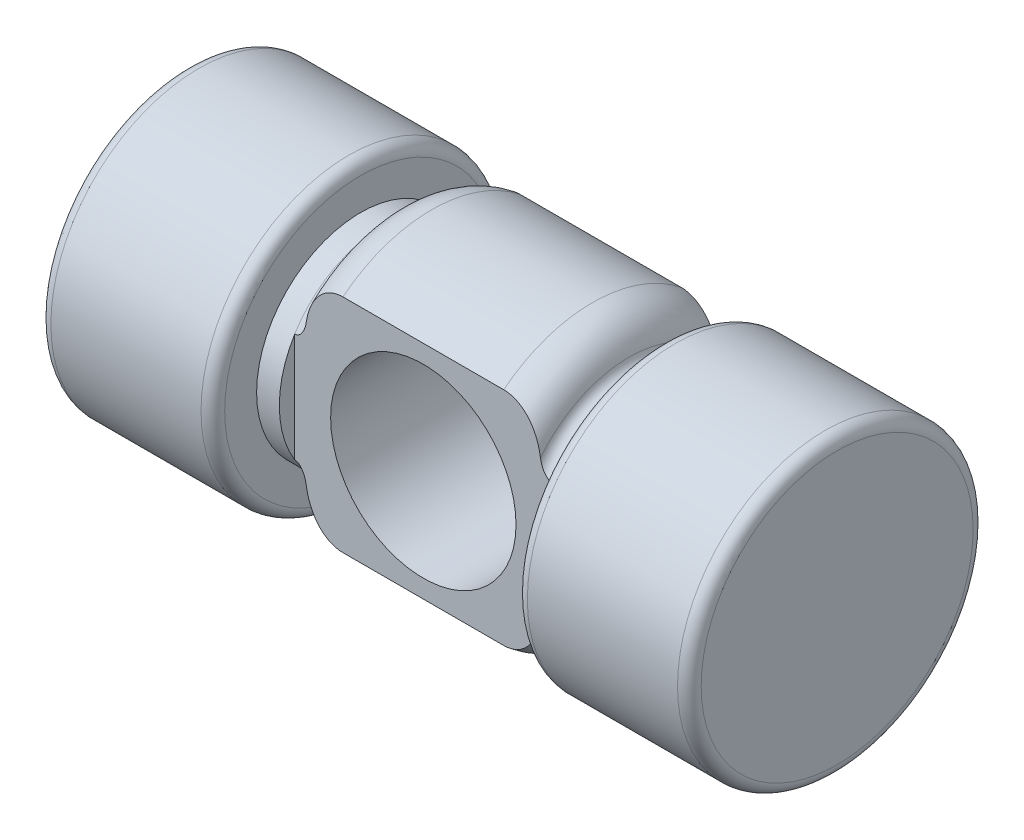
SolidWorks part; units mm, degrees
ref_plane "Front" through (0, 0, 0) normal (0, 0, 1) x (1, 0, 0)
ref_plane "Top" through (0, 0, 0) normal (0, 1, 0) x (1, 0, 0)
ref_plane "Right" through (0, 0, 0) normal (1, 0, 0) x (0, 0, -1)
sketch "Sketch1" plane through (0, 0, 0) normal (0, 0, 1) x (1, 0, 0)
  line L0 (-34.6111, 0) -> (34.1409, 0) construction
  line L1 (-17.4625, 0) -> (17.4625, 0)
  line L2 (17.4625, 0) -> (17.4625, 7.9375)
  line L3 (-6.35, 5.588) -> (-8.128, 5.588)
  line L4 (4.318, 7.62) -> (-4.318, 7.62)
  line L5 (-8.128, 5.588) -> (-8.128, 7.9375)
  line L6 (-17.4625, 7.9375) -> (-17.4625, 0)
  line L7 (0, 0) -> (0, 7.62) construction
  line L8 (-8.128, 7.9375) -> (-17.4625, 7.9375)
  line L9 (6.35, 5.588) -> (8.128, 5.588)
  line L10 (8.128, 5.588) -> (8.128, 7.9375)
  line L11 (8.128, 7.9375) -> (17.4625, 7.9375)
  arc A0 (6.35, 5.588) -> (4.318, 7.62) centre (4.318, 5.588) ccw
  arc A1 (-4.318, 7.62) -> (-6.35, 5.588) centre (-4.318, 5.588) ccw
  dimension "D1" = 34.925
  dimension "D2" = 11.176
  dimension "D3" = 15.875
  dimension "D4" = 15.24
  dimension "D5" = 16.256
  dimension "D6" = 12.7
revolve "Revolve1" add sketch "Sketch1" angle 360 about L0
fillet "Fillet1" radius 0.635 7 edges at (-6.35, 0, 5.588) (6.35, 0, 5.588) (8.128, 0, 5.588) (17.4625, 0, 7.9375) (8.128, 0, 7.9375) (-8.128, 0, 7.9375) (-17.4625, 0, 7.9375)
sketch "Sketch2" plane through (0, 0, 0) normal (0, 1, 0) x (1, 0, 0)
  line L1 (-6.9083, 4.7625) -> (6.9083, 4.7625) construction
  line L2 (-6.9083, 4.7625) -> (-6.9083, -4.7625) construction
  line L3 (-6.9083, -4.7625) -> (6.9083, -4.7625) construction
  line L4 (6.9083, 4.7625) -> (6.9083, -4.7625) construction
  line L5 (-6.9083, 4.7625) -> (6.9083, -4.7625) construction
  line L6 (-6.9083, -4.7625) -> (6.9083, 4.7625) construction
  line L7 (-6.9083, 4.7625) -> (6.9083, 4.7625)
  line L8 (-6.9083, 4.7625) -> (-6.9083, 26.1736)
  line L9 (-6.9083, 26.1736) -> (6.9083, 26.1736)
  line L10 (6.9083, 4.7625) -> (6.9083, 26.1736)
  line L11 (6.9083, -4.7625) -> (-6.9083, -4.7625)
  line L12 (6.9083, -4.7625) -> (6.9083, -25.0311)
  line L13 (6.9083, -25.0311) -> (-6.9083, -25.0311)
  line L14 (-6.9083, -4.7625) -> (-6.9083, -25.0311)
  line L15 (6.9083, -5.588) -> (6.9083, 5.588) construction
  point P0 (0, 0)
  dimension "D2" = 9.525
extrude "Cut-Extrude1" cut sketch "Sketch2" against normal through all and the other way through all
sketch "Sketch3" plane through (0, 0, -4.7625) normal (0, 0, -1) x (-1, 0, 0)
  circle A0 centre (0, 0) radius 4.9784
  dimension "D1" = 9.9568
extrude "Cut-Extrude2" cut sketch "Sketch3" against normal through all
cosmetic thread "Cosmetic Thread1" parameters "D2"=11.1125
